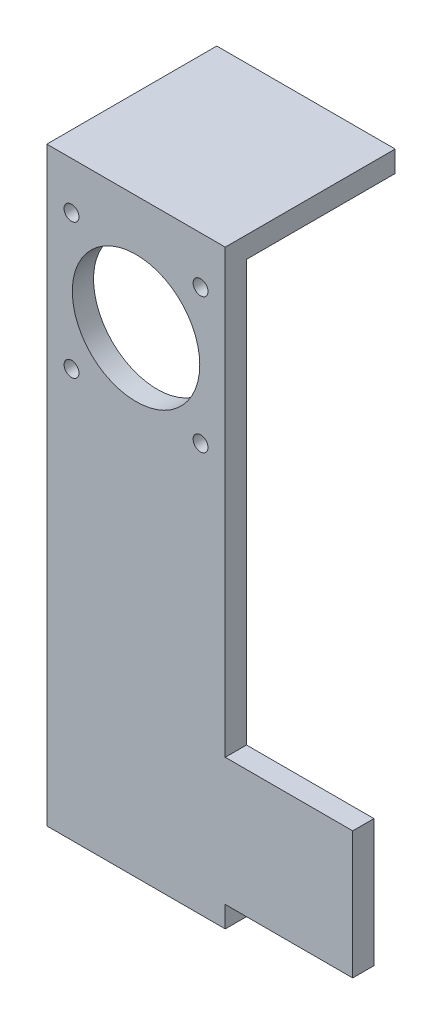
SolidWorks part; units mm, degrees
ref_plane "Front Plane" through (0, 0, 0) normal (0, 0, 1) x (1, 0, 0)
ref_plane "Top Plane" through (0, 0, 0) normal (0, 1, 0) x (1, 0, 0)
ref_plane "Right Plane" through (0, 0, 0) normal (1, 0, 0) x (0, 0, -1)
sketch "Sketch1" plane through (0, 0, 0) normal (0, 0, 1) x (1, 0, 0)
  line L2 (-21, -22) -> (-21, 22)
  line L3 (-21, 22) -> (21, 22)
  line L4 (21, -22) -> (21, 22)
  line L5 (-21, -22) -> (21, 22) construction
  line L6 (-21, 22) -> (21, -22) construction
  line L7 (-21, -22) -> (-21, -112)
  line L8 (21, -22) -> (21, -112)
  line L9 (-21, -112) -> (21, -112)
  line L11 (51, -107) -> (21, -107)
  line L12 (51, -107) -> (51, -77)
  line L13 (51, -77) -> (21, -77)
  line L14 (21, -107) -> (21, -77)
  line L15 (51, -107) -> (21, -77) construction
  line L16 (51, -77) -> (21, -107) construction
  circle A0 centre (0, 0) radius 15
  circle A1 centre (15.1905, 15.9138) radius 1.75
  circle A2 centre (15.1905, -15.9138) radius 1.75
  circle A3 centre (-15.1905, -15.9138) radius 1.75
  circle A4 centre (-15.1905, 15.9138) radius 1.75
  point P0 (0, 0)
  point P16 (36, -92)
  point P25 (118.0878, -100.9344)
  dimension "D4" = 3.5
  dimension "D5" = 3.5
  dimension "D6" = 3.5
  dimension "D7" = 3.5
  dimension "D9" = 22
  dimension "D10" = 22
  dimension "D13" = 30
  dimension "D2" = 42
  dimension "D3" = 44
  dimension "D8" = 22
  dimension "D11" = 22
  dimension "D12" = 90
  dimension "D14" = 42
  dimension "D15" = 90
  dimension "D16" = 44
  dimension "D17" = 30
  dimension "D18" = 30
  dimension "D19" = 20
  dimension "D20" = 15
extrude "Boss-Extrude1" add sketch "Sketch1" along normal blind 5 contours L12 L13 L8 L11 | L7 L9 L8 L4 L3 L2 A4 A3 A2 A1 A0
sketch "Sketch2" plane through (0, 0, 0) normal (0, 0, -1) x (-1, 0, 0)
  line L8 (21, 22) -> (-21, 22) construction
  line L9 (21, 22) -> (-21, 22)
  line L10 (21, 22) -> (21, 27)
  line L11 (21, 27) -> (-21, 27)
  line L12 (-21, 22) -> (-21, 27)
  line L13 (21, 22) -> (-21, 27) construction
  line L14 (21, 27) -> (-21, 22) construction
  line L15 (21, 22) -> (21, -112) construction
  point P0 (0, 24.5)
  dimension "D1" = 0
  dimension "D2" = 42
  dimension "D3" = 21
  dimension "D4" = 5
extrude "Boss-Extrude3" add sketch "Sketch2" against normal blind 5 and the other way blind 35
